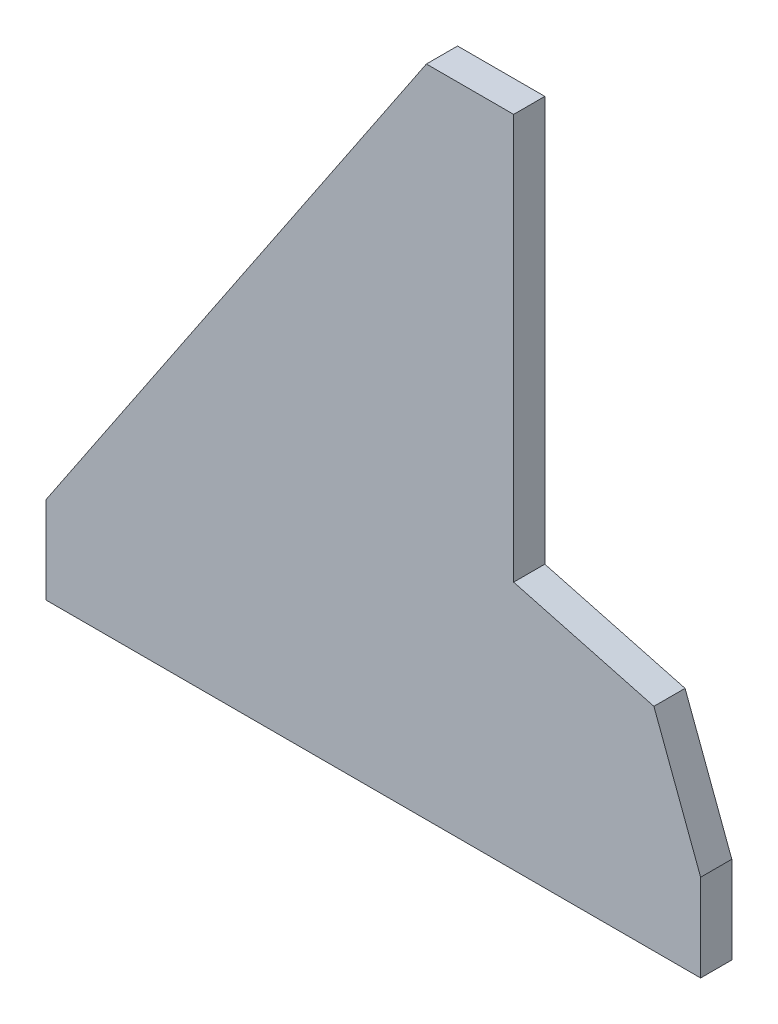
SolidWorks part; units mm, degrees
ref_plane "Ön Düzlem" through (0, 0, 0) normal (0, 0, 1) x (1, 0, 0)
ref_plane "Üst Düzlem" through (0, 0, 0) normal (0, 1, 0) x (1, 0, 0)
ref_plane "Sağ Düzlem" through (0, 0, 0) normal (1, 0, 0) x (0, 0, -1)
sketch "Çizim1" plane through (0, 0, 0) normal (0, 0, 1) x (1, 0, 0)
  line L0 (-210, 28) -> (-210, 0)
  line L1 (-210, 0) -> (0, 0)
  line L2 (0, 0) -> (0, 28)
  line L3 (0, 28) -> (-15, 68)
  line L4 (-15, 68) -> (-60, 80)
  line L5 (-60, 80) -> (-60, 210)
  line L6 (-60, 210) -> (-88, 210)
  line L7 (-88, 210) -> (-210, 28)
  point P2 (-3.7864, 159.0903)
  point P10 (-31.3125, 208)
  point P11 (-11.0273, 78)
  point P12 (48.5335, 51.2944)
  point P13 (-3.6901, 78)
  point P14 (0, 0)
  point P15 (61.1284, 61.5163)
  point P16 (81.6107, 55.6146)
  point P17 (-172.5897, 28)
  point P18 (0, 0)
  point P19 (-210.7478, 0)
  point P20 (-12.0348, 58.0087)
  point P21 (-13.3392, 65.4004)
  point P22 (-85.1948, 210)
  point P23 (-59.0885, 80)
  point P24 (-59.5029, 210)
  point P25 (-13.9204, 68)
  dimension "D1" = 28
  dimension "D2" = 28
  dimension "D3" = 210
  dimension "D4" = 210
  dimension "D5" = 28
  dimension "D6" = 130
  dimension "D7" = 40
  dimension "D8" = 45
  dimension "D9" = 15
extrude "Yükseklik-Ekstrüzyon1" add sketch "Çizim1" along normal blind 10
